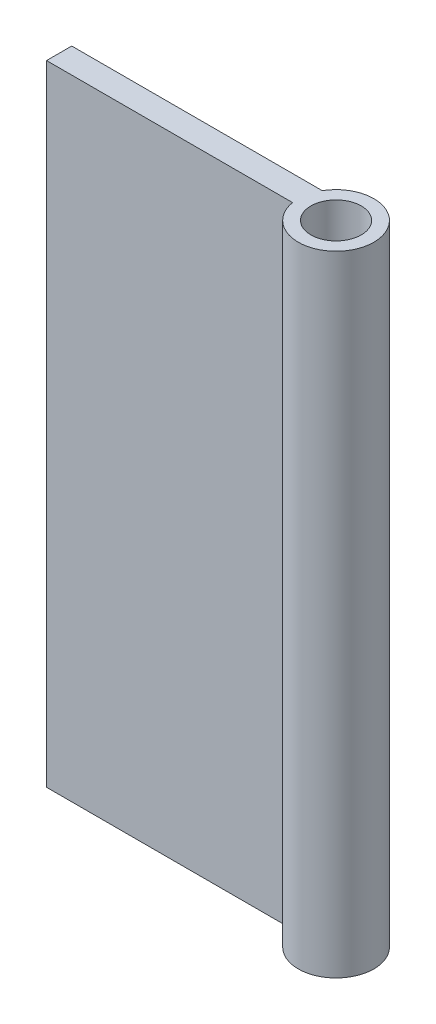
SolidWorks part; units mm, degrees
material "Stainless Steel (ferritic)"
ref_plane "Front Plane" through (0, 0, 0) normal (0, 0, 1) x (1, 0, 0)
ref_plane "Top Plane" through (0, 0, 0) normal (0, 1, 0) x (1, 0, 0)
ref_plane "Right Plane" through (0, 0, 0) normal (1, 0, 0) x (0, 0, -1)
sketch "Sketch3" plane through (0, 0, 0) normal (0, 0, 1) x (1, 0, 0)
  line L1 (-10, -25) -> (10, -25)
  line L2 (-10, -25) -> (-10, 25)
  line L3 (-10, 25) -> (10, 25)
  line L4 (10, -25) -> (10, 25)
  line L5 (-10, -25) -> (10, 25) construction
  line L6 (-10, 25) -> (10, -25) construction
  point P0 (0, 0)
  dimension "D1" = 50
  dimension "D2" = 20
extrude "Boss-Extrude2" add sketch "Sketch3" along normal blind 2
sketch "Sketch4" plane through (0, 25, 0) normal (0, 1, 0) x (1, 0, 0)
  line L0 (10, -2) -> (10, 0) construction
  circle A0 centre (12.5, -1.5) radius 3
  circle A1 centre (12.5, -1.5) radius 2
  dimension "D1" = 6
  dimension "D2" = 2.5
  dimension "D3" = 1
extrude "Boss-Extrude3" add sketch "Sketch4" against normal blind 50
